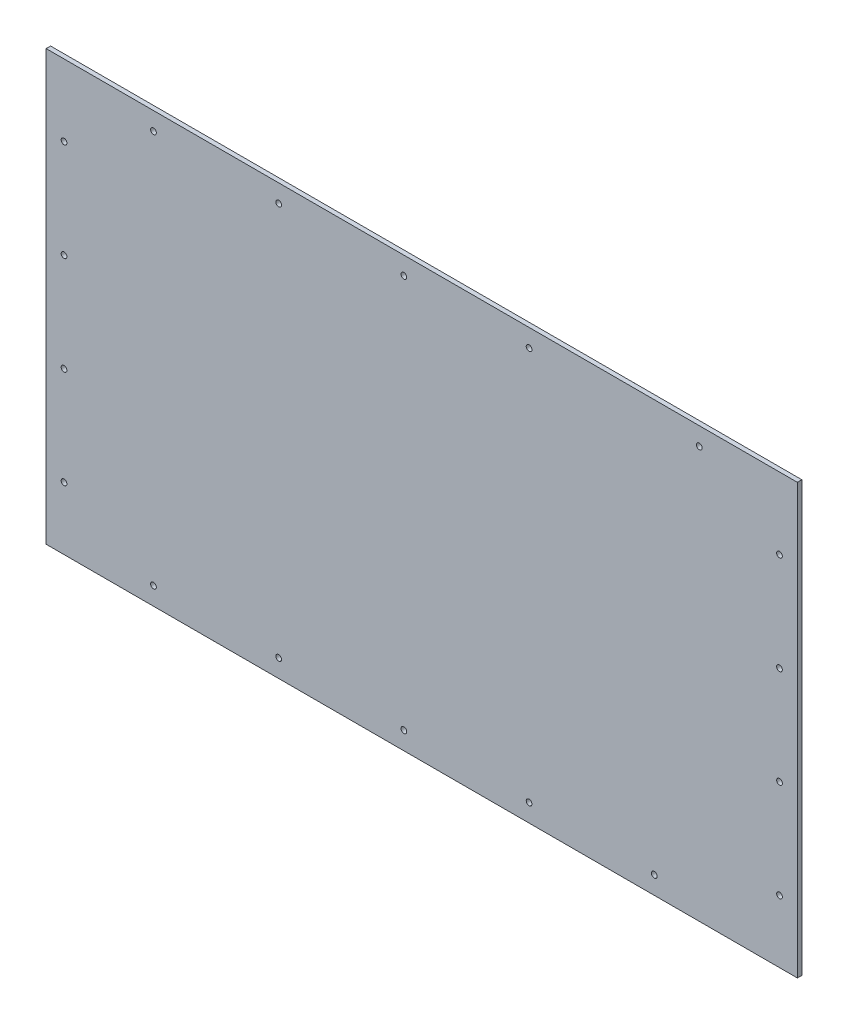
SolidWorks part; units mm, degrees
ref_plane "Front Plane" through (0, 0, 0) normal (0, 0, 1) x (1, 0, 0)
ref_plane "Top Plane" through (0, 0, 0) normal (0, 1, 0) x (1, 0, 0)
ref_plane "Right Plane" through (0, 0, 0) normal (1, 0, 0) x (0, 0, -1)
sketch "Sketch1" plane through (0, 0, 0) normal (0, 0, 1) x (1, 0, 0)
  line L1 (533.4, 0) -> (0, 0)
  line L2 (533.4, 0) -> (533.4, 304.8)
  line L3 (533.4, 304.8) -> (0, 304.8)
  line L4 (0, 0) -> (0, 304.8)
  dimension "D1" = 533.4
  dimension "D2" = 304.8
extrude "Boss-Extrude1" add sketch "Sketch1" along normal blind 3.175
sketch "Sketch5" plane through (0, 0, 3.175) normal (0, 0, 1) x (1, 0, 0)
  line L0 (0, 304.8) -> (0, 0) construction
  line L1 (0, 0) -> (533.4, 0) construction
  line L2 (0, 152.4) -> (533.4, 152.4) construction
  line L3 (533.4, 0) -> (533.4, 304.8) construction
  circle A0 centre (76.2, 12.7) radius 2.032
  circle A1 centre (165.1, 12.7) radius 2.032
  circle A2 centre (254, 12.7) radius 2.032
  circle A3 centre (342.9, 12.7) radius 2.032
  circle A4 centre (431.8, 12.7) radius 2.032
  circle A8 centre (342.9, 292.1) radius 2.032
  circle A9 centre (254, 292.1) radius 2.032
  circle A10 centre (165.1, 292.1) radius 2.032
  circle A11 centre (76.2, 292.1) radius 2.032
  circle A12 centre (463.7195, 292.1) radius 2.032
  circle A13 centre (520.7, 12.7) radius 2.032 [skipped]
  dimension "D1" = 4.064
  dimension "D2" = 76.2
  dimension "D5" = 88.9
  dimension "D7" = 4.064
  dimension "D4" = 12.7
  dimension "D3" = 6
extrude "Cut-Extrude4" cut sketch "Sketch5" against normal through all
sketch "Sketch6" plane through (0, 0, 3.175) normal (0, 0, 1) x (1, 0, 0)
  line L0 (0, 304.8) -> (0, 0) construction
  line L1 (533.4, 304.8) -> (0, 304.8) construction
  line L2 (266.7, 304.8) -> (266.7, 0) construction
  line L3 (0, 0) -> (533.4, 0) construction
  circle A0 centre (12.7, 254) radius 2.032
  circle A1 centre (12.7, 184.15) radius 2.032
  circle A2 centre (12.7, 114.3) radius 2.032
  circle A3 centre (12.7, 44.45) radius 2.032
  circle A4 centre (520.7, 44.45) radius 2.032
  circle A5 centre (520.7, 114.3) radius 2.032
  circle A6 centre (520.7, 184.15) radius 2.032
  circle A7 centre (520.7, 254) radius 2.032
  dimension "D1" = 4.064
  dimension "D3" = 50.8
  dimension "D5" = 69.85
  dimension "D2" = 12.7
  dimension "D4" = 4
extrude "Cut-Extrude5" cut sketch "Sketch6" against normal blind 3.175
